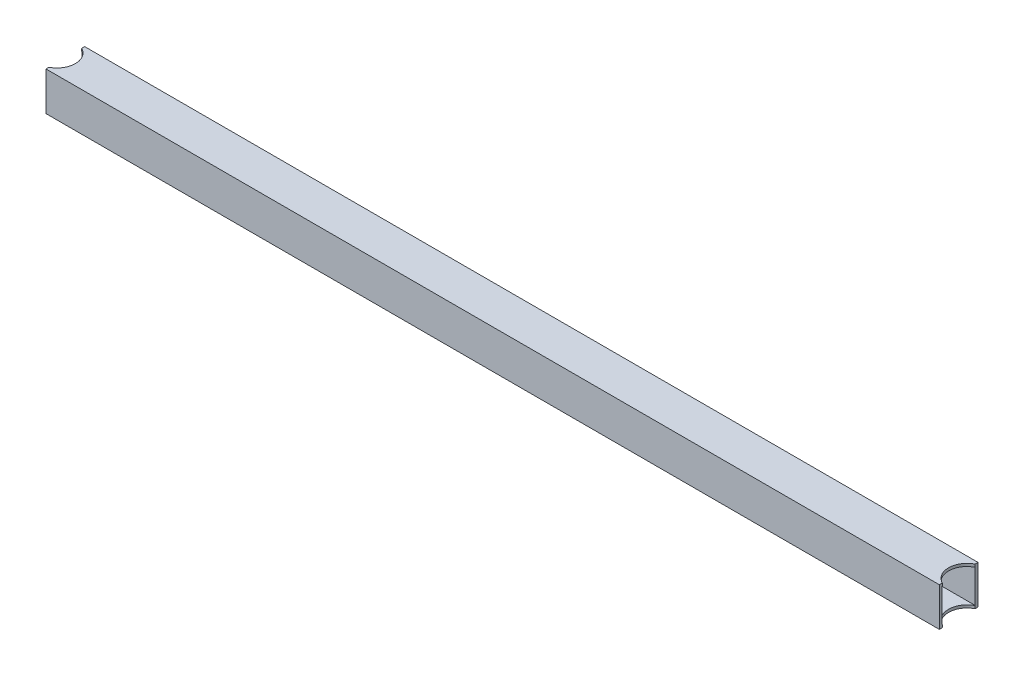
SolidWorks part; units mm, degrees
material "6061 Alloy"
ref_plane "Front Plane" through (0, 0, 0) normal (0, 0, 1) x (1, 0, 0)
ref_plane "Top Plane" through (0, 0, 0) normal (0, 1, 0) x (1, 0, 0)
ref_plane "Right Plane" through (0, 0, 0) normal (1, 0, 0) x (0, 0, -1)
sketch "Sketch2" plane through (0, 0, 0) normal (0, 1, 0) x (1, 0, 0)
  line L0 (522.605, 0) -> (-522.605, 0) construction
  line L1 (0, 22.225) -> (0, -22.225) construction
  line L2 (513.08, 22.225) -> (-513.08, 22.225)
  line L3 (-513.08, 22.225) -> (-513.08, 18.8076)
  line L4 (-513.08, -22.225) -> (-513.08, -18.8076)
  line L5 (513.08, -22.225) -> (-513.08, -22.225)
  line L6 (513.08, -22.225) -> (513.08, -18.8076)
  line L7 (513.08, 22.225) -> (513.08, 18.8076)
  circle A0 centre (-522.605, 0) radius 21.082
  circle A1 centre (522.605, 0) radius 21.082
  dimension "D2" = 42.164
  dimension "D1" = 44.45
  dimension "D3" = 9.525
  dimension "D4" = 3.4174
  dimension "D5" = 1026.16
extrude "Boss-Extrude1" add sketch "Sketch2" along normal blind 44.45 contours L6 A1 L7 L2 L3 A0 L4 L5
sketch "Sketch3" plane through (-513.08, 0, 0) normal (-1, 0, 0) x (0, 0, 1)
  line L0 (-19.05, 3.175) -> (-19.05, 41.275)
  line L1 (-22.225, 0) -> (22.225, 0) construction
  line L2 (-22.225, 0) -> (-22.225, 44.45) construction
  line L3 (-22.225, 44.45) -> (22.225, 44.45) construction
  line L4 (22.225, 0) -> (22.225, 44.45) construction
  line L5 (-19.05, 41.275) -> (19.05, 41.275)
  line L6 (19.05, 3.175) -> (19.05, 41.275)
  line L7 (-19.05, 3.175) -> (19.05, 3.175)
  dimension "D1" = 3.175
extrude "Cut-Extrude1" cut sketch "Sketch3" against normal through all
